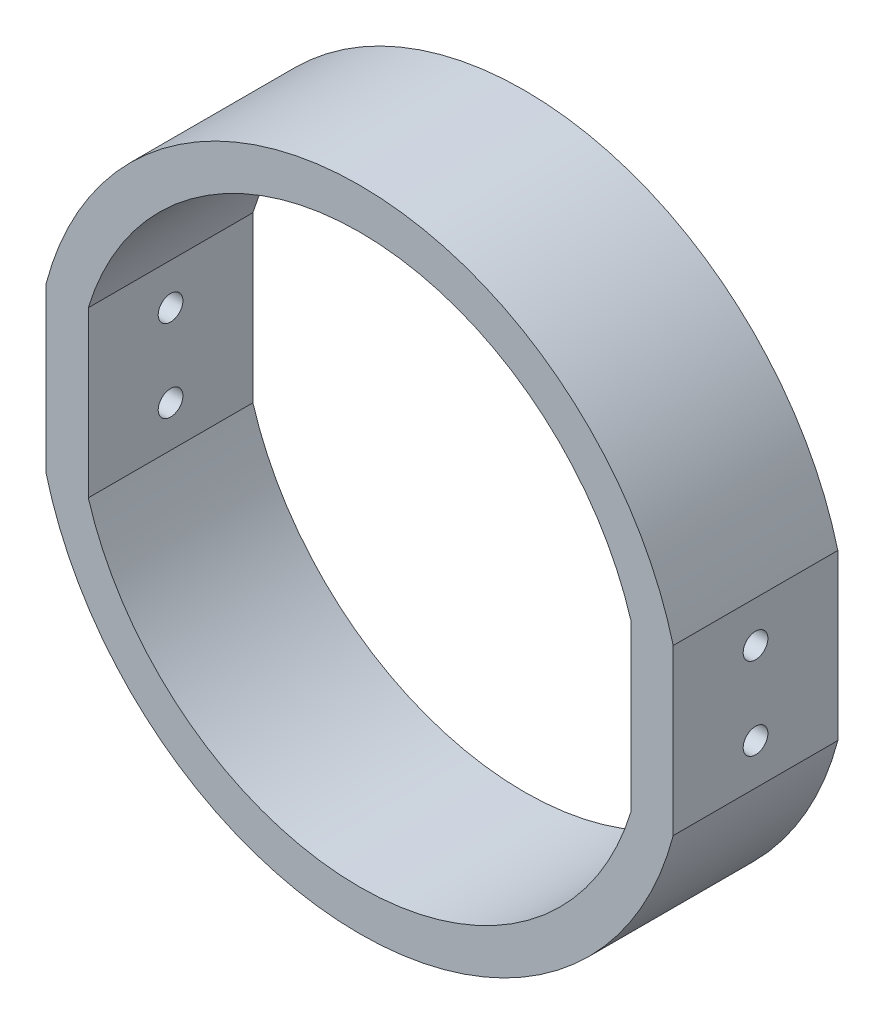
SolidWorks part; units mm, degrees
ref_plane "Front Plane" through (0, 0, 0) normal (0, 0, 1) x (1, 0, 0)
ref_plane "Top Plane" through (0, 0, 0) normal (0, 1, 0) x (1, 0, 0)
ref_plane "Right Plane" through (0, 0, 0) normal (1, 0, 0) x (0, 0, -1)
sketch "Sketch1" plane through (0, 0, 0) normal (0, 0, 1) x (1, 0, 0)
  line L0 (34.0944, 0) -> (-34.0944, 0) construction
  line L1 (0, 39.3818) -> (0, -39.3818) construction
  line L2 (-21.2793, 0) -> (-21.2793, 10) construction
  line L3 (38.091, 0) -> (39.0631, 0) construction
  line L4 (21.2793, 0) -> (21.2793, 10) construction
  line L5 (-38.091, 0) -> (-39.0631, 0) construction
  line L6 (-32.9762, 10) -> (-32.9762, -10)
  line L7 (38.091, 10) -> (38.091, -10)
  line L8 (32.9762, 10) -> (32.9762, -10)
  line L9 (-38.091, 10) -> (-38.091, -10)
  line L10 (-38.091, 10) -> (-32.9762, 10) construction
  arc A0 (-32.9762, -10) -> (32.9762, -10) centre (0, 0) ccw
  arc A1 (-38.091, -10) -> (38.091, -10) centre (0, 0) ccw
  arc A2 (38.091, 10) -> (-38.091, 10) centre (0, 0) ccw
  arc A3 (32.9762, 10) -> (-32.9762, 10) centre (0, 0) ccw
  dimension "D1" = 10
  dimension "D2" = 39.3818
  dimension "D3" = 5.1149
extrude "Boss-Extrude1" add sketch "Sketch1" along normal blind 20
sketch "Sketch3" plane through (38.091, 0, 0) normal (1, 0, 0) x (0, 0, -1)
  line L0 (0, 0) -> (-20, 0) construction
  line L1 (-20, -10) -> (-20, 10) construction
  line L2 (-10, 10) -> (-10, -10) construction
  line L3 (-20, 10) -> (0, 10) construction
  line L4 (-20, -10) -> (0, -10) construction
  circle A0 centre (-10, 5) radius 1.5
  circle A1 centre (-10, -5) radius 1.5
extrude "Cut-Extrude2" cut sketch "Sketch3" against normal through all
